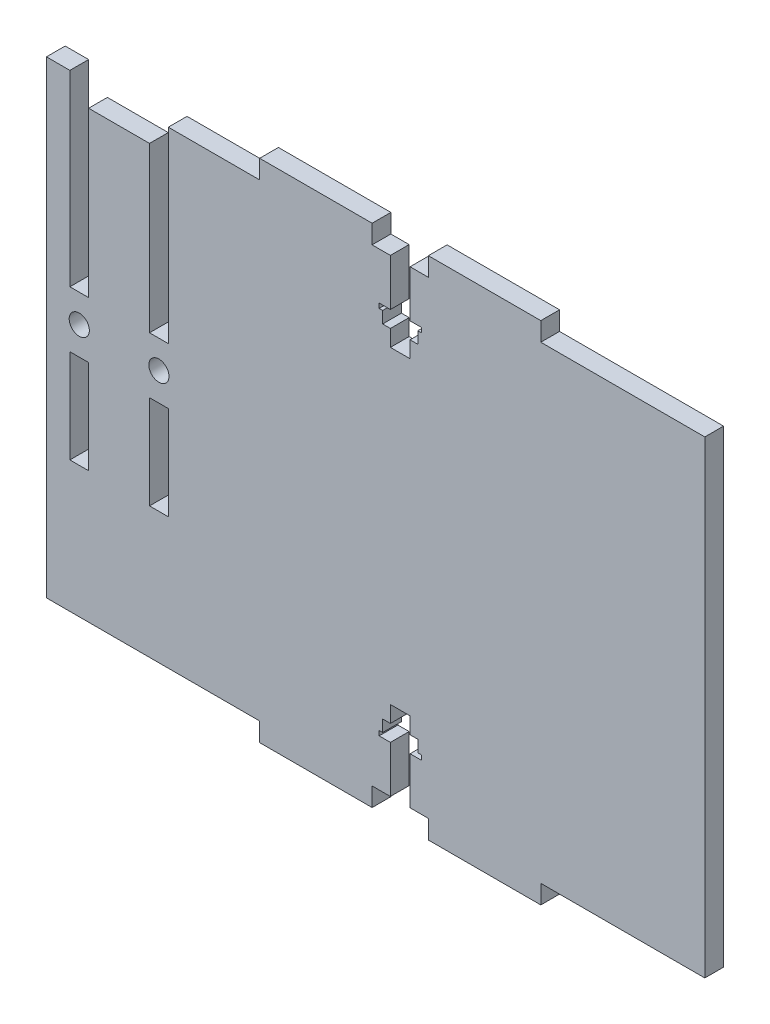
SolidWorks part; units mm, degrees
ref_plane "Front Plane" through (0, 0, 0) normal (0, 0, 1) x (1, 0, 0)
ref_plane "Top Plane" through (0, 0, 0) normal (0, 1, 0) x (1, 0, 0)
ref_plane "Right Plane" through (0, 0, 0) normal (1, 0, 0) x (0, 0, -1)
sketch "Sketch1" plane through (0, 0, 0) normal (0, 0, 1) x (1, 0, 0)
  line L1 (-125, 50) -> (125, 50)
  line L2 (-125, 50) -> (-125, -50)
  line L3 (-125, -50) -> (125, -50)
  line L4 (125, 50) -> (125, -50)
  line L5 (-125, 50) -> (125, -50) construction
  line L6 (-125, -50) -> (125, 50) construction
  point P0 (0, 0)
  dimension "D1" = 250
  dimension "D2" = 100
extrude "Boss-Extrude1" add sketch "Sketch1" along normal blind 4
sketch "Sketch2" plane through (0, -50, 0) normal (0, -1, 0) x (1, 0, 0)
  line L0 (-125, 4) -> (125, 4) construction
  line L1 (-66, 4) -> (-90, 4)
  line L2 (-66, 4) -> (-66, 0)
  line L3 (-66, 0) -> (-90, 0)
  line L4 (-90, 4) -> (-90, 0)
  line L5 (-125, 0) -> (125, 0) construction
  line L7 (-54, 4) -> (-30, 4)
  line L8 (-54, 4) -> (-54, 0)
  line L9 (-54, 0) -> (-30, 0)
  line L10 (-30, 4) -> (-30, 0)
  line L11 (-125, 4) -> (-125, 0) construction
  line L12 (0, 0) -> (0, 4) construction
  line L13 (30, 4) -> (30, 0)
  line L14 (54, 0) -> (30, 0)
  line L15 (54, 4) -> (54, 0)
  line L16 (54, 4) -> (30, 4)
  line L17 (90, 4) -> (90, 0)
  line L18 (66, 0) -> (90, 0)
  line L19 (66, 4) -> (66, 0)
  line L20 (66, 4) -> (90, 4)
  dimension "D1" = 24
  dimension "D2" = 35
  dimension "D3" = 12
  dimension "D4" = 24
extrude "Boss-Extrude2" add sketch "Sketch2" along normal blind 4
sketch "Sketch3" plane through (0, 0, 4) normal (0, 0, 1) x (1, 0, 0)
  line L0 (-8.5, 50) -> (-8.5, -50) construction
  line L1 (125, 50) -> (-125, 50) construction
  line L2 (-30, -50) -> (30, -50) construction
  line L3 (0, 50) -> (0, -50) construction
  line L4 (-10.5, 50) -> (-6.5, 50)
  line L5 (-10.5, 50) -> (-10.5, 10)
  line L6 (-10.5, 10) -> (-6.5, 10)
  line L7 (-6.5, 50) -> (-6.5, 10)
  line L8 (-10.5, 50) -> (-6.5, 10) construction
  line L9 (-10.5, 10) -> (-6.5, 50) construction
  line L10 (-10.5, -2) -> (-6.5, -2)
  line L11 (-10.5, -2) -> (-10.5, -22)
  line L12 (-10.5, -22) -> (-6.5, -22)
  line L13 (-6.5, -2) -> (-6.5, -22)
  line L14 (-10.5, -2) -> (-6.5, -22) construction
  line L15 (-10.5, -22) -> (-6.5, -2) construction
  line L16 (10.5, -22) -> (6.5, -2) construction
  line L17 (10.5, -2) -> (6.5, -22) construction
  line L18 (10.5, 10) -> (6.5, 50) construction
  line L19 (10.5, 50) -> (6.5, 10) construction
  line L20 (6.5, -2) -> (6.5, -22)
  line L21 (10.5, -22) -> (6.5, -22)
  line L22 (10.5, -2) -> (10.5, -22)
  line L23 (10.5, -2) -> (6.5, -2)
  line L24 (6.5, 50) -> (6.5, 10)
  line L25 (10.5, 10) -> (6.5, 10)
  line L26 (10.5, 50) -> (10.5, 10)
  line L27 (10.5, 50) -> (6.5, 50)
  point P6 (-8.5, 30)
  point P11 (-8.5, -12)
  point P26 (8.5, -12)
  point P27 (8.5, 30)
  dimension "D1" = 4
  dimension "D2" = 28
  dimension "D3" = 12
  dimension "D4" = 6.5
  dimension "D5" = 20
extrude "Cut-Extrude1" cut sketch "Sketch3" against normal through all
mirror "Mirror1" about plane through (0, 0, 0) normal (0, 1, 0) of "Boss-Extrude2"
hole_wizard "M4 Clearance Hole1" positions "Sketch5" profile "Sketch4" hole size "M4" standard "DIN"
sketch "Sketch5" plane through (0, 0, 4) normal (0, 0, 1) x (1, 0, 0)
  line L0 (-8.5, 10) -> (-8.5, -2) construction
  line L1 (-10.5, 10) -> (-6.5, 10) construction
  line L2 (-6.5, -2) -> (-10.5, -2) construction
  line L4 (8.5, 10) -> (8.5, -2) construction
  line L5 (6.5, 10) -> (10.5, 10) construction
  line L6 (10.5, -2) -> (6.5, -2) construction
  point P0 (-8.5, 4)
  point P19 (8.5, 4)
sketch "Sketch4" plane through (-8.5, 4, 4) normal (1, 0, 0) x (0, -1, 0)
  line L0 (0, 0) -> (0, 7.2919)
  line L1 (0, 7.2919) -> (2.15, 6)
  line L2 (2.15, 6) -> (2.15, 0)
  line L5 (2.15, 0) -> (0, 0)
  line L10 (0, 7.2919) -> (-2.15, 6) construction
  line L11 (0, -6.35) -> (0, 107.95) construction
  dimension "Hole Dia." = 4.3
  dimension "Hole Depth" = 6
  dimension "Drill Angle" = 118
sketch "Sketch6" plane through (0, 0, 4) normal (0, 0, 1) x (1, 0, 0)
  line L0 (-66, -50) -> (-54, -50) construction
  line L1 (60, -50) -> (60, -33) construction
  line L2 (57.9, -50) -> (57.9, -40)
  line L3 (62.1, -50) -> (62.1, -40)
  line L4 (56.25, -36.5) -> (57.9, -36.5)
  line L5 (56.25, -36.5) -> (56.25, -39)
  line L6 (62.1, -36.5) -> (62.1, -33)
  line L7 (63.75, -36.5) -> (63.75, -39)
  line L8 (55.5, -39) -> (55.5, -40)
  line L9 (64.5, -40) -> (62.1, -40)
  line L10 (62.1, -40) -> (64.5, -40)
  line L12 (0, 0) -> (0, -50) construction
  line L13 (-30, -50) -> (30, -50) construction
  line L14 (0, 0) -> (-125, 0) construction
  line L15 (-125, 50) -> (-125, -50) construction
  line L16 (64.5, -39) -> (64.5, -40)
  line L17 (64.5, -39) -> (63.75, -39)
  line L18 (62.1, -36.5) -> (62.1, -33)
  line L19 (63.75, -39) -> (64.5, -39)
  line L20 (57.9, -36.5) -> (56.25, -36.5)
  line L21 (56.25, -39) -> (55.5, -39)
  line L22 (62.1, -36.5) -> (63.75, -36.5)
  line L23 (57.9, -36.5) -> (57.9, -33)
  line L24 (57.9, -40) -> (55.5, -40)
  line L25 (56.25, -36.5) -> (56.25, -39)
  line L26 (57.9, -36.5) -> (57.9, -33)
  line L27 (55.5, -39) -> (56.25, -39)
  line L28 (55.5, -39) -> (55.5, -40)
  line L29 (55.5, -40) -> (57.9, -40)
  line L30 (64.5, -39) -> (64.5, -40)
  line L31 (63.75, -36.5) -> (63.75, -39)
  line L32 (63.75, -36.5) -> (62.1, -36.5)
  line L33 (57.9, -50) -> (57.9, -40)
  line L34 (62.1, -50) -> (62.1, -40)
  line L35 (57.9, -50) -> (57.9, -40)
  line L36 (62.1, -50) -> (62.1, -40)
  line L37 (56.25, -36.5) -> (57.9, -36.5)
  line L38 (56.25, -36.5) -> (56.25, -39)
  line L39 (55.5, -39) -> (55.5, -40)
  line L40 (64.5, -40) -> (62.1, -40)
  line L41 (64.5, -39) -> (64.5, -40)
  line L42 (64.5, -39) -> (63.75, -39)
  line L43 (62.1, -36.5) -> (62.1, -33)
  line L44 (63.75, -36.5) -> (63.75, -39)
  line L45 (62.1, -40) -> (64.5, -40)
  line L46 (62.1, -36.5) -> (62.1, -33)
  line L47 (57.9, -36.5) -> (56.25, -36.5)
  line L48 (63.75, -39) -> (64.5, -39)
  line L49 (-62.1, -50) -> (-57.9, -50)
  line L50 (-62.1, -50) -> (-62.1, -40)
  line L51 (-62.1, -33) -> (-57.9, -33)
  line L52 (-57.9, -50) -> (-57.9, -40)
  line L53 (-60, -50) -> (-60, -33) construction
  line L54 (-63.75, -36.5) -> (-62.1, -36.5)
  line L55 (-63.75, -36.5) -> (-63.75, -39)
  line L56 (-57.9, -36.5) -> (-57.9, -33)
  line L57 (-56.25, -36.5) -> (-56.25, -39)
  line L58 (-64.5, -39) -> (-64.5, -40)
  line L59 (-55.5, -40) -> (-57.9, -40)
  line L60 (-57.9, -40) -> (-55.5, -40)
  line L61 (-55.5, -39) -> (-55.5, -40)
  line L62 (-55.5, -39) -> (-56.25, -39)
  line L63 (-57.9, -36.5) -> (-57.9, -33)
  line L64 (-56.25, -39) -> (-55.5, -39)
  line L65 (-62.1, -36.5) -> (-63.75, -36.5)
  line L66 (-63.75, -39) -> (-64.5, -39)
  line L67 (-57.9, -36.5) -> (-56.25, -36.5)
  line L68 (-62.1, -36.5) -> (-62.1, -33)
  line L69 (-62.1, -40) -> (-64.5, -40)
  line L70 (-63.75, -36.5) -> (-63.75, -39)
  line L71 (-62.1, -36.5) -> (-62.1, -33)
  line L72 (-64.5, -39) -> (-63.75, -39)
  line L73 (-64.5, -39) -> (-64.5, -40)
  line L74 (-64.5, -40) -> (-62.1, -40)
  line L75 (-55.5, -39) -> (-55.5, -40)
  line L76 (-56.25, -36.5) -> (-56.25, -39)
  line L77 (-56.25, -36.5) -> (-57.9, -36.5)
  line L78 (-62.1, -50) -> (-62.1, -40)
  line L79 (-57.9, -50) -> (-57.9, -40)
  line L80 (-62.1, -50) -> (-62.1, -40)
  line L81 (-57.9, -50) -> (-57.9, -40)
  line L82 (-63.75, -36.5) -> (-62.1, -36.5)
  line L83 (-63.75, -36.5) -> (-63.75, -39)
  line L84 (-64.5, -39) -> (-64.5, -40)
  line L85 (-55.5, -40) -> (-57.9, -40)
  line L86 (-55.5, -39) -> (-55.5, -40)
  line L87 (-55.5, -39) -> (-56.25, -39)
  line L88 (-57.9, -36.5) -> (-57.9, -33)
  line L89 (-56.25, -36.5) -> (-56.25, -39)
  line L90 (-57.9, -40) -> (-55.5, -40)
  line L91 (-57.9, -36.5) -> (-57.9, -33)
  line L92 (-62.1, -36.5) -> (-63.75, -36.5)
  line L93 (-56.25, -39) -> (-55.5, -39)
  line L94 (-57.9, -36.5) -> (-56.25, -36.5)
  line L95 (-63.75, -39) -> (-64.5, -39)
  line L96 (-62.1, -36.5) -> (-62.1, -33)
  line L97 (-64.5, -39) -> (-63.75, -39)
  line L98 (-64.5, -39) -> (-64.5, -40)
  line L99 (-62.1, -40) -> (-64.5, -40)
  line L100 (-64.5, -40) -> (-62.1, -40)
  line L101 (-55.5, -39) -> (-55.5, -40)
  line L102 (-63.75, -36.5) -> (-63.75, -39)
  line L103 (-62.1, -36.5) -> (-62.1, -33)
  line L104 (-56.25, -36.5) -> (-56.25, -39)
  line L105 (-56.25, -36.5) -> (-57.9, -36.5)
  line L106 (-62.1, -50) -> (-62.1, -40)
  line L107 (-57.9, -50) -> (-57.9, -40)
  line L108 (62.1, -36.5) -> (63.75, -36.5)
  line L109 (56.25, -39) -> (55.5, -39)
  line L110 (57.9, -36.5) -> (57.9, -33)
  line L111 (55.5, -39) -> (56.25, -39)
  line L112 (55.5, -39) -> (55.5, -40)
  line L113 (57.9, -40) -> (55.5, -40)
  line L114 (55.5, -40) -> (57.9, -40)
  line L115 (64.5, -39) -> (64.5, -40)
  line L116 (56.25, -36.5) -> (56.25, -39)
  line L117 (57.9, -36.5) -> (57.9, -33)
  line L118 (63.75, -36.5) -> (63.75, -39)
  line L119 (63.75, -36.5) -> (62.1, -36.5)
  line L120 (57.9, -50) -> (57.9, -40)
  line L121 (62.1, -33) -> (57.9, -33)
  line L122 (62.1, -50) -> (62.1, -40)
  line L123 (62.1, -50) -> (57.9, -50)
  line L124 (-62.1, -50) -> (-62.1, -40)
  line L125 (-57.9, -50) -> (-57.9, -40)
  line L126 (-63.75, -36.5) -> (-62.1, -36.5)
  line L127 (-63.75, -36.5) -> (-63.75, -39)
  line L128 (-57.9, -36.5) -> (-57.9, -33)
  line L129 (-56.25, -36.5) -> (-56.25, -39)
  line L130 (-64.5, -39) -> (-64.5, -40)
  line L131 (-55.5, -40) -> (-57.9, -40)
  line L132 (-57.9, -40) -> (-55.5, -40)
  line L133 (-55.5, -39) -> (-55.5, -40)
  line L134 (-55.5, -39) -> (-56.25, -39)
  line L135 (-57.9, -36.5) -> (-57.9, -33)
  line L136 (-56.25, -39) -> (-55.5, -39)
  line L137 (-62.1, -36.5) -> (-63.75, -36.5)
  line L138 (-63.75, -39) -> (-64.5, -39)
  line L139 (-57.9, -36.5) -> (-56.25, -36.5)
  line L140 (-62.1, -36.5) -> (-62.1, -33)
  line L141 (-62.1, -40) -> (-64.5, -40)
  line L142 (-63.75, -36.5) -> (-63.75, -39)
  line L143 (-62.1, -36.5) -> (-62.1, -33)
  line L144 (-64.5, -39) -> (-63.75, -39)
  line L145 (-64.5, -39) -> (-64.5, -40)
  line L146 (-64.5, -40) -> (-62.1, -40)
  line L147 (-55.5, -39) -> (-55.5, -40)
  line L148 (-56.25, -36.5) -> (-56.25, -39)
  line L149 (-56.25, -36.5) -> (-57.9, -36.5)
  line L150 (-62.1, -50) -> (-62.1, -40)
  line L151 (-57.9, -50) -> (-57.9, -40)
  line L152 (-62.1, -50) -> (-62.1, -40)
  line L153 (-57.9, -50) -> (-57.9, -40)
  line L154 (-63.75, -36.5) -> (-62.1, -36.5)
  line L155 (-63.75, -36.5) -> (-63.75, -39)
  line L156 (-64.5, -39) -> (-64.5, -40)
  line L157 (-55.5, -40) -> (-57.9, -40)
  line L158 (-55.5, -39) -> (-55.5, -40)
  line L159 (-55.5, -39) -> (-56.25, -39)
  line L160 (-57.9, -36.5) -> (-57.9, -33)
  line L161 (-56.25, -36.5) -> (-56.25, -39)
  line L162 (-57.9, -40) -> (-55.5, -40)
  line L163 (-57.9, -36.5) -> (-57.9, -33)
  line L164 (-62.1, -36.5) -> (-63.75, -36.5)
  line L165 (-56.25, -39) -> (-55.5, -39)
  line L166 (-57.9, -36.5) -> (-56.25, -36.5)
  line L167 (-63.75, -39) -> (-64.5, -39)
  line L168 (-62.1, -36.5) -> (-62.1, -33)
  line L169 (-64.5, -39) -> (-63.75, -39)
  line L170 (-64.5, -39) -> (-64.5, -40)
  line L171 (-62.1, -40) -> (-64.5, -40)
  line L172 (-64.5, -40) -> (-62.1, -40)
  line L173 (-55.5, -39) -> (-55.5, -40)
  line L174 (-63.75, -36.5) -> (-63.75, -39)
  line L175 (-62.1, -36.5) -> (-62.1, -33)
  line L176 (-56.25, -36.5) -> (-56.25, -39)
  line L177 (-56.25, -36.5) -> (-57.9, -36.5)
  line L178 (-62.1, -50) -> (-62.1, -40)
  line L179 (-57.9, -50) -> (-57.9, -40)
  line L180 (60, 50) -> (60, 33) construction
  line L181 (62.1, 50) -> (57.9, 50)
  line L182 (62.1, 50) -> (62.1, 40)
  line L183 (62.1, 33) -> (57.9, 33)
  line L184 (57.9, 50) -> (57.9, 40)
  line L185 (63.75, 36.5) -> (62.1, 36.5)
  line L186 (63.75, 36.5) -> (63.75, 39)
  line L187 (57.9, 36.5) -> (57.9, 33)
  line L188 (56.25, 36.5) -> (56.25, 39)
  line L189 (64.5, 39) -> (64.5, 40)
  line L190 (55.5, 40) -> (57.9, 40)
  line L191 (57.9, 40) -> (55.5, 40)
  line L192 (55.5, 39) -> (55.5, 40)
  line L193 (55.5, 39) -> (56.25, 39)
  line L194 (57.9, 36.5) -> (57.9, 33)
  line L195 (56.25, 39) -> (55.5, 39)
  line L196 (62.1, 36.5) -> (63.75, 36.5)
  line L197 (63.75, 39) -> (64.5, 39)
  line L198 (57.9, 36.5) -> (56.25, 36.5)
  line L199 (62.1, 36.5) -> (62.1, 33)
  line L200 (62.1, 40) -> (64.5, 40)
  line L201 (63.75, 36.5) -> (63.75, 39)
  line L202 (62.1, 36.5) -> (62.1, 33)
  line L203 (64.5, 39) -> (63.75, 39)
  line L204 (64.5, 39) -> (64.5, 40)
  line L205 (64.5, 40) -> (62.1, 40)
  line L206 (55.5, 39) -> (55.5, 40)
  line L207 (56.25, 36.5) -> (56.25, 39)
  line L208 (56.25, 36.5) -> (57.9, 36.5)
  line L209 (62.1, 50) -> (62.1, 40)
  line L210 (57.9, 50) -> (57.9, 40)
  line L211 (62.1, 50) -> (62.1, 40)
  line L212 (57.9, 50) -> (57.9, 40)
  line L213 (63.75, 36.5) -> (62.1, 36.5)
  line L214 (63.75, 36.5) -> (63.75, 39)
  line L215 (64.5, 39) -> (64.5, 40)
  line L216 (55.5, 40) -> (57.9, 40)
  line L217 (55.5, 39) -> (55.5, 40)
  line L218 (55.5, 39) -> (56.25, 39)
  line L219 (57.9, 36.5) -> (57.9, 33)
  line L220 (56.25, 36.5) -> (56.25, 39)
  line L221 (57.9, 40) -> (55.5, 40)
  line L222 (57.9, 36.5) -> (57.9, 33)
  line L223 (62.1, 36.5) -> (63.75, 36.5)
  line L224 (56.25, 39) -> (55.5, 39)
  line L225 (57.9, 36.5) -> (56.25, 36.5)
  line L226 (63.75, 39) -> (64.5, 39)
  line L227 (62.1, 36.5) -> (62.1, 33)
  line L228 (64.5, 39) -> (63.75, 39)
  line L229 (64.5, 39) -> (64.5, 40)
  line L230 (62.1, 40) -> (64.5, 40)
  line L231 (64.5, 40) -> (62.1, 40)
  line L232 (55.5, 39) -> (55.5, 40)
  line L233 (63.75, 36.5) -> (63.75, 39)
  line L234 (62.1, 36.5) -> (62.1, 33)
  line L235 (56.25, 36.5) -> (56.25, 39)
  line L236 (56.25, 36.5) -> (57.9, 36.5)
  line L237 (62.1, 50) -> (62.1, 40)
  line L238 (57.9, 50) -> (57.9, 40)
  line L239 (-60, 50) -> (-60, 33) construction
  line L240 (-57.9, 50) -> (-57.9, 40)
  line L241 (-62.1, 50) -> (-62.1, 40)
  line L242 (-56.25, 36.5) -> (-57.9, 36.5)
  line L243 (-56.25, 36.5) -> (-56.25, 39)
  line L244 (-62.1, 36.5) -> (-62.1, 33)
  line L245 (-63.75, 36.5) -> (-63.75, 39)
  line L246 (-55.5, 39) -> (-55.5, 40)
  line L247 (-64.5, 40) -> (-62.1, 40)
  line L248 (-62.1, 40) -> (-64.5, 40)
  line L249 (-64.5, 39) -> (-64.5, 40)
  line L250 (-64.5, 39) -> (-63.75, 39)
  line L251 (-62.1, 36.5) -> (-62.1, 33)
  line L252 (-63.75, 39) -> (-64.5, 39)
  line L253 (-57.9, 36.5) -> (-56.25, 36.5)
  line L254 (-56.25, 39) -> (-55.5, 39)
  line L255 (-62.1, 36.5) -> (-63.75, 36.5)
  line L256 (-57.9, 36.5) -> (-57.9, 33)
  line L257 (-57.9, 40) -> (-55.5, 40)
  line L258 (-56.25, 36.5) -> (-56.25, 39)
  line L259 (-57.9, 36.5) -> (-57.9, 33)
  line L260 (-55.5, 39) -> (-56.25, 39)
  line L261 (-55.5, 39) -> (-55.5, 40)
  line L262 (-55.5, 40) -> (-57.9, 40)
  line L263 (-64.5, 39) -> (-64.5, 40)
  line L264 (-63.75, 36.5) -> (-63.75, 39)
  line L265 (-63.75, 36.5) -> (-62.1, 36.5)
  line L266 (-57.9, 50) -> (-57.9, 40)
  line L267 (-62.1, 50) -> (-62.1, 40)
  line L268 (-57.9, 50) -> (-57.9, 40)
  line L269 (-62.1, 50) -> (-62.1, 40)
  line L270 (-56.25, 36.5) -> (-57.9, 36.5)
  line L271 (-56.25, 36.5) -> (-56.25, 39)
  line L272 (-55.5, 39) -> (-55.5, 40)
  line L273 (-64.5, 40) -> (-62.1, 40)
  line L274 (-64.5, 39) -> (-64.5, 40)
  line L275 (-64.5, 39) -> (-63.75, 39)
  line L276 (-62.1, 36.5) -> (-62.1, 33)
  line L277 (-63.75, 36.5) -> (-63.75, 39)
  line L278 (-62.1, 40) -> (-64.5, 40)
  line L279 (-62.1, 36.5) -> (-62.1, 33)
  line L280 (-57.9, 36.5) -> (-56.25, 36.5)
  line L281 (-63.75, 39) -> (-64.5, 39)
  line L282 (-62.1, 36.5) -> (-63.75, 36.5)
  line L283 (-56.25, 39) -> (-55.5, 39)
  line L284 (-57.9, 36.5) -> (-57.9, 33)
  line L285 (-55.5, 39) -> (-56.25, 39)
  line L286 (-55.5, 39) -> (-55.5, 40)
  line L287 (-57.9, 40) -> (-55.5, 40)
  line L288 (-55.5, 40) -> (-57.9, 40)
  line L289 (-64.5, 39) -> (-64.5, 40)
  line L290 (-56.25, 36.5) -> (-56.25, 39)
  line L291 (-57.9, 36.5) -> (-57.9, 33)
  line L292 (-63.75, 36.5) -> (-63.75, 39)
  line L293 (-63.75, 36.5) -> (-62.1, 36.5)
  line L294 (-57.9, 50) -> (-57.9, 40)
  line L295 (-62.1, 50) -> (-62.1, 40)
  line L296 (-57.9, 50) -> (-57.9, 40)
  line L297 (-62.1, 50) -> (-62.1, 40)
  line L298 (-56.25, 36.5) -> (-57.9, 36.5)
  line L299 (-56.25, 36.5) -> (-56.25, 39)
  line L300 (-62.1, 36.5) -> (-62.1, 33)
  line L301 (-63.75, 36.5) -> (-63.75, 39)
  line L302 (-55.5, 39) -> (-55.5, 40)
  line L303 (-64.5, 40) -> (-62.1, 40)
  line L304 (-62.1, 40) -> (-64.5, 40)
  line L305 (-64.5, 39) -> (-64.5, 40)
  line L306 (-64.5, 39) -> (-63.75, 39)
  line L307 (-62.1, 36.5) -> (-62.1, 33)
  line L308 (-63.75, 39) -> (-64.5, 39)
  line L309 (-57.9, 36.5) -> (-56.25, 36.5)
  line L310 (-56.25, 39) -> (-55.5, 39)
  line L311 (-62.1, 36.5) -> (-63.75, 36.5)
  line L312 (-57.9, 36.5) -> (-57.9, 33)
  line L313 (-57.9, 40) -> (-55.5, 40)
  line L314 (-56.25, 36.5) -> (-56.25, 39)
  line L315 (-57.9, 36.5) -> (-57.9, 33)
  line L316 (-55.5, 39) -> (-56.25, 39)
  line L317 (-55.5, 39) -> (-55.5, 40)
  line L318 (-55.5, 40) -> (-57.9, 40)
  line L319 (-64.5, 39) -> (-64.5, 40)
  line L320 (-63.75, 36.5) -> (-63.75, 39)
  line L321 (-63.75, 36.5) -> (-62.1, 36.5)
  line L322 (-57.9, 50) -> (-57.9, 40)
  line L323 (-62.1, 50) -> (-62.1, 40)
  line L324 (-57.9, 50) -> (-57.9, 40)
  line L325 (-62.1, 50) -> (-62.1, 40)
  line L326 (-56.25, 36.5) -> (-57.9, 36.5)
  line L327 (-56.25, 36.5) -> (-56.25, 39)
  line L328 (-55.5, 39) -> (-55.5, 40)
  line L329 (-64.5, 40) -> (-62.1, 40)
  line L330 (-64.5, 39) -> (-64.5, 40)
  line L331 (-64.5, 39) -> (-63.75, 39)
  line L332 (-62.1, 36.5) -> (-62.1, 33)
  line L333 (-63.75, 36.5) -> (-63.75, 39)
  line L334 (-62.1, 40) -> (-64.5, 40)
  line L335 (-62.1, 36.5) -> (-62.1, 33)
  line L336 (-57.9, 36.5) -> (-56.25, 36.5)
  line L337 (-63.75, 39) -> (-64.5, 39)
  line L338 (-62.1, 36.5) -> (-63.75, 36.5)
  line L339 (-56.25, 39) -> (-55.5, 39)
  line L340 (-57.9, 36.5) -> (-57.9, 33)
  line L341 (-55.5, 39) -> (-56.25, 39)
  line L342 (-55.5, 39) -> (-55.5, 40)
  line L343 (-57.9, 40) -> (-55.5, 40)
  line L344 (-55.5, 40) -> (-57.9, 40)
  line L345 (-64.5, 39) -> (-64.5, 40)
  line L346 (-56.25, 36.5) -> (-56.25, 39)
  line L347 (-57.9, 36.5) -> (-57.9, 33)
  line L348 (-63.75, 36.5) -> (-63.75, 39)
  line L349 (-63.75, 36.5) -> (-62.1, 36.5)
  line L350 (-57.9, 50) -> (-57.9, 40)
  line L351 (-62.1, 33) -> (-57.9, 33)
  line L352 (-62.1, 50) -> (-62.1, 40)
  line L353 (-62.1, 50) -> (-57.9, 50)
  dimension "D2" = 10
  dimension "D6" = 4.2
  dimension "D7" = 17
  dimension "D8" = 7.5
  dimension "D9" = 2.5
  dimension "D10" = 9
  dimension "D11" = 1
extrude "Cut-Extrude2" cut sketch "Sketch6" against normal blind 10
sketch "Sketch7" plane through (0, 0, 4) normal (0, 0, 1) x (1, 0, 0)
  line L0 (6.5, 50) -> (6.5, 10) construction
  line L1 (-6.5, 50) -> (6.5, 50)
  line L2 (-6.5, 50) -> (-6.5, 45)
  line L3 (-6.5, 45) -> (6.5, 45)
  line L4 (6.5, 50) -> (6.5, 45)
  dimension "D1" = 5
extrude "Cut-Extrude3" cut sketch "Sketch7" against normal blind 10
sketch "Sketch8" plane through (0, 0, 4) normal (0, 0, 1) x (1, 0, 0)
  line L0 (-15.5, 50) -> (-32.7004, 262.6981)
  line L1 (-10.5, 50) -> (-30, 50) construction
  line L2 (-15.5, 50) -> (-15.5, -103.3951)
  line L3 (-15.5, -103.3951) -> (-171.9994, -88.1497)
  line L4 (-171.9994, -88.1497) -> (-161.8358, 81.1134)
  line L5 (-32.7004, 262.6981) -> (-161.8358, 81.1134)
extrude "Cut-Extrude4" cut sketch "Sketch8" against normal blind 10
